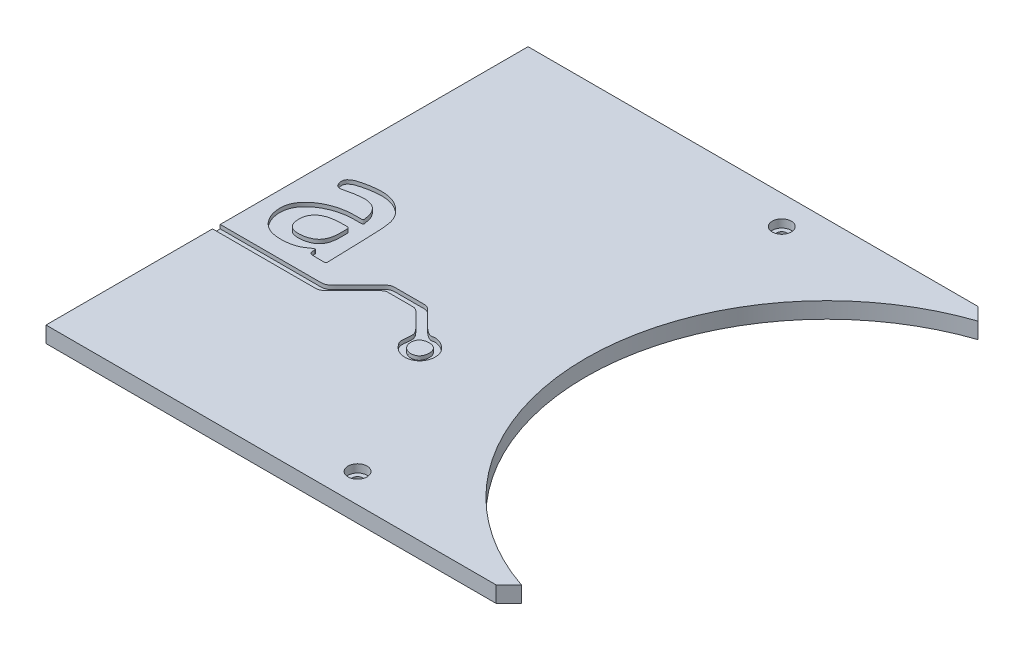
SolidWorks part; units mm, degrees
other "Marca1"
sketch "Croquis4" plane through (-24, 5, 75) normal (0.0144, 0.9293, 0.3691) x (0.9999, -0.0163, 0.0019)
material "PLA"
ref_plane "Alzado" through (0, 0, 0) normal (0, 0, 1) x (1, 0, 0)
ref_plane "Planta" through (0, 0, 0) normal (0, 1, 0) x (1, 0, 0)
ref_plane "Vista lateral" through (0, 0, 0) normal (1, 0, 0) x (0, 0, -1)
sketch "Croquis1" plane through (0, 0, 0) normal (0, 1, 0) x (1, 0, 0)
  line L0 (-327.9437, 75) -> (-327.9437, -75)
  line L1 (-327.9437, 75) -> (-27.9437, 75)
  line L2 (-27.9437, 75) -> (-24, 71.0563)
  line L3 (-327.9437, -75) -> (-27.9437, -75)
  line L4 (-27.9437, -75) -> (-24, -71.0563)
  circle A0 centre (0, 0) radius 75 construction
  arc A1 (-24, 71.0563) -> (-24, -71.0563) centre (0, 0) ccw
  point P6 (-327.9437, 0)
  point P11 (-75, 0)
  dimension "D1" = 150
  dimension "D2" = 150
  dimension "D3" = 300
  dimension "D4" = 135
  dimension "D5" = 24
extrude "Saliente-Extruir1" add sketch "Croquis1" along normal blind 5 contours L1 L2 A1 L4 L3 L0
sketch "Croquis2" plane through (0, 5, 0) normal (0, 1, 0) x (1, 0, 0)
  line L0 (-327.9437, 75) -> (-27.9437, 75) construction
  line L1 (-327.9437, -75) -> (-27.9437, -75) construction
  line L2 (-327.9437, 75) -> (-327.9437, -75) construction
  circle A0 centre (-318.9437, 0) radius 1.6
  circle A1 centre (-240.0037, 66) radius 1.6
  circle A2 centre (-240.0037, -66) radius 1.6
  circle A3 centre (-80.0037, -66) radius 1.6
  circle A4 centre (-80.0037, 66) radius 1.6
  dimension "D1" = 3.2
  dimension "D2" = 9
  dimension "D3" = 9
  dimension "D4" = 9
  dimension "D5" = 160
  dimension "D6" = 87.94
extrude "Cortar-Extruir1" cut sketch "Croquis2" against normal blind 5
sketch "Croquis3" plane through (0, 5, 0) normal (0, 1, 0) x (1, 0, 0)
  circle A0 centre (-240.0037, -66) radius 2.95
  circle A1 centre (-80.0037, -66) radius 2.95
  circle A2 centre (-80.0037, 66) radius 2.95
  circle A3 centre (-240.0037, 66) radius 2.95
  circle A4 centre (-318.9437, 0) radius 2.95
  dimension "D1" = 5.9
extrude "Cortar-Extruir2" cut sketch "Croquis3" against normal blind 2.5
sketch "Croquis5" plane through (0, 5, 0) normal (0, 1, 0) x (1, 0, 0)
  spline S0 degree 3 number of poles 565 (-264.8912, -10.407) -> (-264.8912, -10.407)
  spline S1 degree 3 number of poles 279 (-262.6484, 48.2089) -> (-262.6484, 48.2089)
  spline S2 degree 3 number of poles 493 (-213.5311, -14.7576) -> (-213.5311, -14.7576)
  spline S3 degree 3 number of poles 157 (-225.2653, -4.52) -> (-225.2653, -4.52)
  spline S4 degree 3 number of poles 343 (-98.8163, -23.8618) -> (-98.8163, -23.8618)
  spline S5 degree 3 number of poles 343 (-189.9262, 10.8546) -> (-189.9262, 10.8546)
  spline S6 degree 3 number of poles 380 (-145.717, -14.6405) -> (-145.717, -14.6405)
  spline S7 degree 3 number of poles 125 (-156.8594, -5.2926) -> (-156.8594, -5.2926)
  spline S8 degree 3 number of poles 123 (-242.4618, 21.9905) -> (-242.4618, 21.9905)
  spline S9 degree 3 poles (-242.3565, -0.9911) (-242.3565, 3.3839) (-242.3565, 7.7589) (-242.3565, 12.1339) (-242.3565, 12.24) (-242.3565, 12.4521) (-242.7133, 12.8089) (-242.9254, 12.8089) (-243.0315, 12.8089) (-243.7065, 12.8089) (-244.3815, 12.8089) (-245.0565, 12.8089) (-245.7315, 12.8089) (-246.4065, 12.8089) (-247.0815, 12.8089) (-247.1876, 12.8089) (-247.3997, 12.8089) (-247.7565, 12.4521) (-247.7565, 12.24) (-247.7565, 12.1339) (-247.7565, 7.7589) (-247.7565, 3.3839) (-247.7565, -0.9911) (-247.7565, -5.3661) (-247.7565, -9.7411) (-247.7565, -14.1161) (-247.7565, -14.2221) (-247.7565, -14.4343) (-247.3997, -14.7911) (-247.1876, -14.7911) (-247.0815, -14.7911) (-246.4065, -14.7911) (-245.7315, -14.7911) (-245.0565, -14.7911) (-244.3815, -14.7911) (-243.7065, -14.7911) (-243.0315, -14.7911) (-242.9254, -14.7911) (-242.7133, -14.7911) (-242.3565, -14.4343) (-242.3565, -14.2221) (-242.3565, -14.1161) (-242.3565, -9.7411) (-242.3565, -5.3661) (-242.3565, -0.9911) (-242.3565, 3.3839) (-242.3565, 7.7589) knots -0.203746 0 0 0 0.203746 0.203746 0.203746 0.208686 0.213625 0.218565 0.218565 0.218565 0.25 0.25 0.25 0.281435 0.281435 0.281435 0.286375 0.291314 0.296254 0.296254 0.296254 0.5 0.5 0.5 0.703746 0.703746 0.703746 0.708686 0.713625 0.718565 0.718565 0.718565 0.75 0.75 0.75 0.781435 0.781435 0.781435 0.786375 0.791314 0.796254 0.796254 0.796254 1 1 1 1.203746 1.203746 1.203746 only from (-242.3565, -0.9911) to (-242.3565, -0.9911)
  spline S10 degree 3 number of poles 99 (-100.9338, -21.7323) -> (-100.9338, -21.7323)
extrude "Cortar-Extruir3" cut sketch "Croquis5" against normal blind 1.2
sketch "Croquis6" plane through (0, 5, 0) normal (0, 1, 0) x (1, 0, 0)
  line L0 (-327.9437, 75) -> (-327.9437, -75) construction
  line L1 (-167.9437, -102.5037) -> (-367.9437, -102.5037)
  line L2 (-167.9437, -102.5037) -> (-167.9437, 97.4963)
  line L3 (-167.9437, 97.4963) -> (-367.9437, 97.4963)
  line L4 (-367.9437, -102.5037) -> (-367.9437, 97.4963)
  line L5 (-167.9437, -102.5037) -> (-367.9437, 97.4963) construction
  line L6 (-167.9437, 97.4963) -> (-367.9437, -102.5037) construction
  point P0 (-267.9437, -2.5037)
  dimension "D1" = 160
  dimension "D2" = 200
  dimension "D3" = 200
extrude "Cortar-Extruir4" cut sketch "Croquis6" against normal blind 10
sketch "Croquis7" plane through (0, 0, 0) normal (0, -1, 0) x (1, 0, 0)
  line L0 (-167.9437, 75) -> (-167.9437, -75) construction
  line L1 (-155.4437, 45) -> (-180.4437, 45)
  line L2 (-155.4437, 45) -> (-155.4437, 65)
  line L3 (-155.4437, 65) -> (-180.4437, 65)
  line L4 (-180.4437, 45) -> (-180.4437, 65)
  line L5 (-155.4437, 45) -> (-180.4437, 65) construction
  line L6 (-155.4437, 65) -> (-180.4437, 45) construction
  line L7 (-167.9437, 75) -> (-27.9437, 75) construction
  line L8 (-155.4437, -65) -> (-180.4437, -65)
  line L9 (-155.4437, -65) -> (-155.4437, -45)
  line L10 (-155.4437, -45) -> (-180.4437, -45)
  line L11 (-180.4437, -65) -> (-180.4437, -45)
  line L12 (-155.4437, -65) -> (-180.4437, -45) construction
  line L13 (-155.4437, -45) -> (-180.4437, -65) construction
  line L14 (-167.9437, -75) -> (-27.9437, -75) construction
  point P0 (-167.9437, 55)
  point P7 (-167.9437, -55)
  dimension "D1" = 10
  dimension "D2" = 10
  dimension "D3" = 25
  dimension "D4" = 20
extrude "Cortar-Extruir5" cut sketch "Croquis7" against normal blind 2.5
